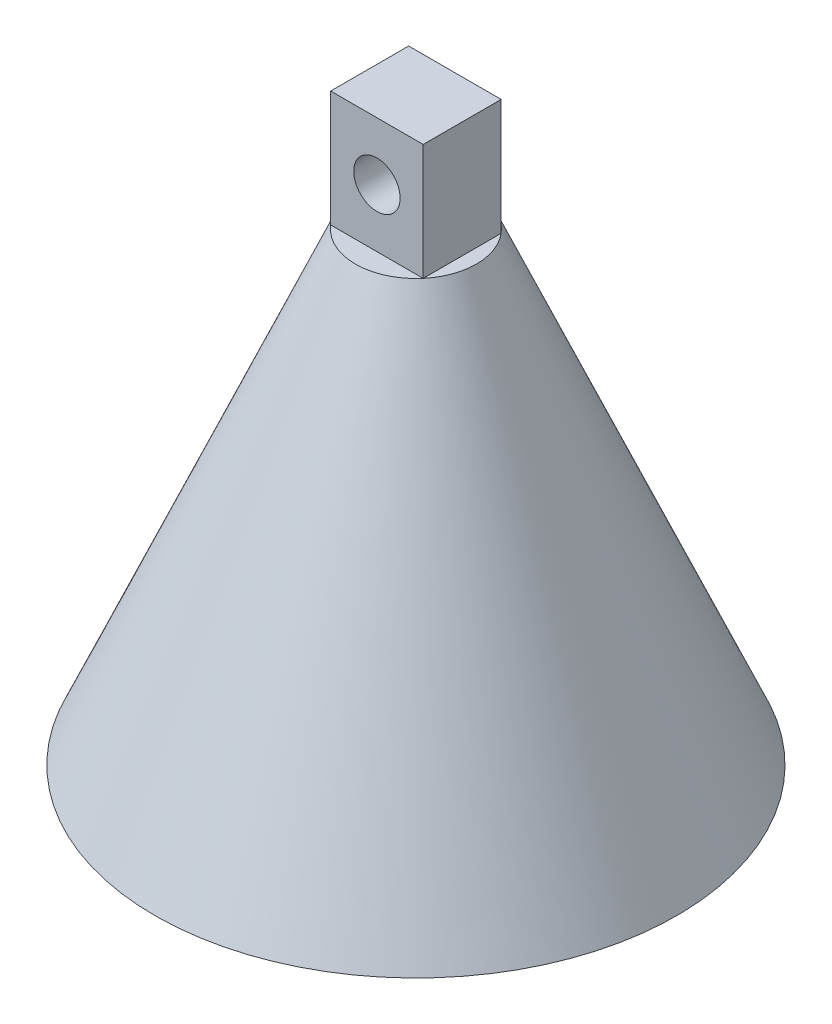
SolidWorks part; units mm, degrees
ref_plane "Plan de face" through (0, 0, 0) normal (0, 0, 1) x (1, 0, 0)
ref_plane "Plan de dessus" through (0, 0, 0) normal (0, 1, 0) x (1, 0, 0)
ref_plane "Plan de droite" through (0, 0, 0) normal (1, 0, 0) x (0, 0, -1)
sketch "Esquisse1" plane through (0, 0, 0) normal (0, 0, 1) x (1, 0, 0)
  line L0 (0, 0) -> (2, 0)
  line L1 (2, 0) -> (19.2851, 40)
  line L2 (19.2851, 40) -> (22.5, 40)
  line L3 (0, 0) -> (17.2851, 40)
  line L4 (17.2851, 40) -> (19.2851, 40)
  line L5 (22.5, 40) -> (22.5, 0) construction
  line L6 (18.1451, 37.3619) -> (22.5, 37.3619)
  line L7 (22.5, 37.3619) -> (22.5, 40)
  dimension "D1" = 22.5
  dimension "D2" = 2
  dimension "D3" = 40
revolve "Révolution1" add sketch "Esquisse1" angle 360 about L5
sketch "Esquisse2" plane through (0, 40, 0) normal (0, 1, 0) x (1, 0, 0)
  line L1 (26.4876, 3.3606) -> (18.5124, 3.3606)
  line L2 (26.4876, 3.3606) -> (26.4876, -3.3606)
  line L3 (26.4876, -3.3606) -> (18.5124, -3.3606)
  line L4 (18.5124, 3.3606) -> (18.5124, -3.3606)
  line L5 (26.4876, 3.3606) -> (18.5124, -3.3606) construction
  line L6 (26.4876, -3.3606) -> (18.5124, 3.3606) construction
  circle A0 centre (22.5, 0) radius 5.2149 construction
  point P0 (22.5, 0)
extrude "Boss.-Extru.1" add sketch "Esquisse2" along normal blind 10 contours L1 L4 L3 L2
sketch "Esquisse3" plane through (0, 0, -3.3606) normal (0, 0, -1) x (-1, 0, 0)
  line L0 (-26.4876, 50) -> (-26.4876, 40) construction
  line L1 (-18.5124, 50) -> (-18.5124, 40) construction
  line L2 (-26.4876, 45) -> (-18.5124, 45)
  circle A0 centre (-22.5, 45) radius 2
  point P0 (-26.4876, 45)
  point P1 (-18.5124, 45)
  point P8 (-22.5, 45)
extrude "Enlèv. mat.-Extru.1" cut sketch "Esquisse3" against normal blind 13 and the other way blind 14 contours L2 A0 | L2 A0
